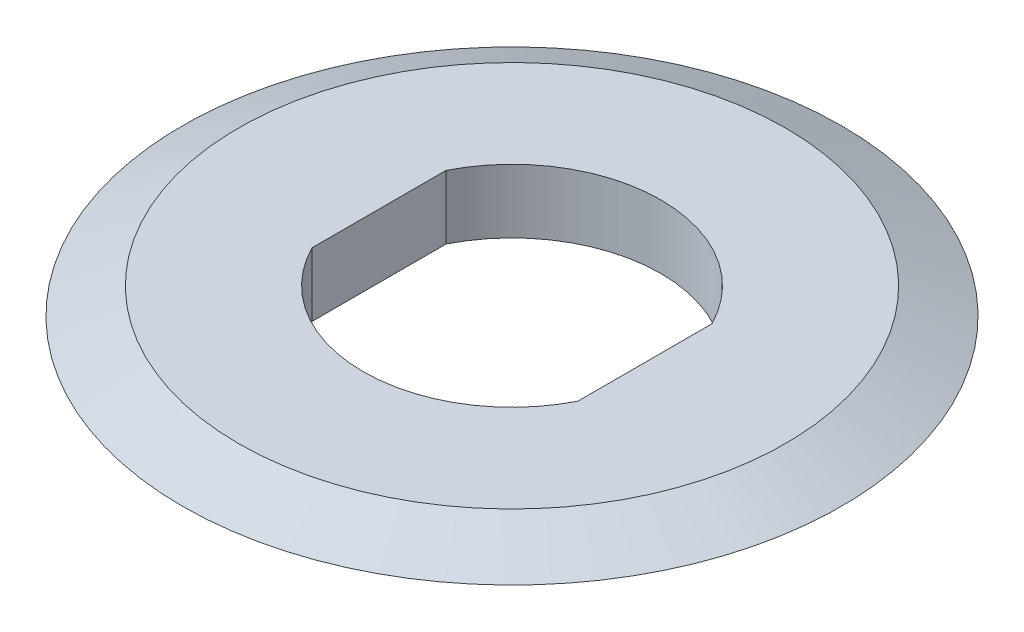
SolidWorks part; units mm, degrees
material "1060 Alloy"
ref_plane "Front Plane" through (0, 0, 0) normal (0, 0, 1) x (1, 0, 0)
ref_plane "Top Plane" through (0, 0, 0) normal (0, 1, 0) x (1, 0, 0)
ref_plane "Right Plane" through (0, 0, 0) normal (1, 0, 0) x (0, 0, -1)
sketch "Sketch2" plane through (0, 0, 0) normal (0, 1, 0) x (1, 0, 0)
  circle A0 centre (0, 0) radius 9.92
  dimension "D1" = 19.84
extrude "Boss-Extrude1" add sketch "Sketch2" along normal mid plane 1.92
sketch "Sketch3" plane through (0, 0, 0) normal (0, 0, 1) x (1, 0, 0)
  line L0 (-9.92, 0.96) -> (-8.23, 0.96)
  line L1 (9.92, 0.96) -> (-9.92, 0.96) construction
  line L2 (-8.23, 0.96) -> (8.23, 0.96)
  line L3 (8.23, 0.96) -> (9.92, 0.96)
  line L4 (-9.92, 0.96) -> (-9.92, 0.1719)
  line L5 (-9.92, 0.96) -> (-9.92, -0.96) construction
  line L6 (-9.92, 0.1719) -> (-8.23, 0.96)
  line L7 (-9.92, -0.96) -> (-7.4925, -0.96)
  line L8 (-9.92, -0.96) -> (9.92, -0.96) construction
  line L9 (-7.4925, -0.96) -> (7.4925, -0.96)
  line L10 (7.4925, -0.96) -> (9.92, -0.96)
  line L12 (-7.5, 0.96) -> (-8.23, 0.96)
  line L13 (0, 0) -> (0, 2.122) construction
  line L14 (-8.23, 0.96) -> (-9.92, 0.96)
  line L15 (-9.92, 0.1719) -> (-9.92, -0.96)
  line L16 (-9.92, 0.1719) -> (-7.4925, -0.96)
  line L17 (-9.92, 0.1719) -> (-9.1308, 0.1719) construction
  point P16 (0, -0.96)
  dimension "D1" = 16.46
  dimension "D2" = 25
  dimension "D3" = 25
revolve "Cut-Revolve3" cut sketch "Sketch3" angle 360 about L13
sketch "Sketch4" plane through (0, 0.96, 0) normal (0, 1, 0) x (1, 0, 0)
  line L0 (4, 0) -> (4, 2.0175)
  line L1 (4, 0) -> (4, -2.0175)
  line L2 (0, 0) -> (0, 10.3801) construction
  line L3 (-4, 0) -> (-4, -2.0175)
  line L4 (-4, 0) -> (-4, 2.0175)
  arc A0 (4, 2.0175) -> (-4, 2.0175) centre (0, 0) ccw
  arc A2 (-4, -2.0175) -> (4, -2.0175) centre (0, 0) ccw
  dimension "D1" = 8.96
extrude "Cut-Extrude2" cut sketch "Sketch4" against normal blind 1.92
fillet "Fillet1" radius 5 1 edges at (0, -0.96, -7.4925)
